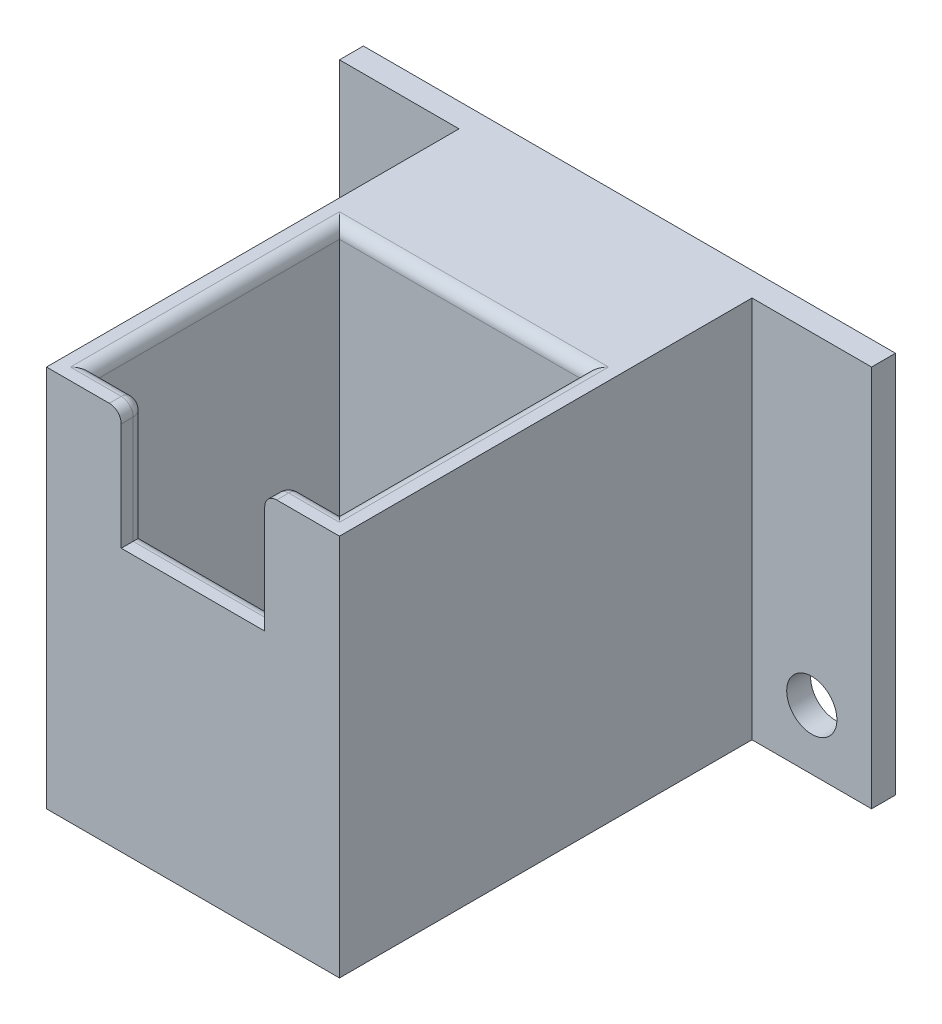
SolidWorks part; units mm, degrees
ref_plane "Plan de face" through (0, 0, 0) normal (0, 0, 1) x (1, 0, 0)
ref_plane "Plan de dessus" through (0, 0, 0) normal (0, 1, 0) x (1, 0, 0)
ref_plane "Plan de droite" through (0, 0, 0) normal (1, 0, 0) x (0, 0, -1)
sketch "Esquisse1" plane through (0, 0, 0) normal (0, 1, 0) x (1, 0, 0)
  line L1 (0, 0) -> (24.5, 0)
  line L2 (0, 0) -> (0, 34.5)
  line L3 (0, 36.5) -> (24.5, 36.5)
  line L4 (24.5, 0) -> (24.5, 34.5)
  line L5 (2, 22.5) -> (22.5, 22.5)
  line L6 (2, 22.5) -> (2, 2)
  line L7 (2, 2) -> (22.5, 2)
  line L8 (22.5, 22.5) -> (22.5, 2)
  line L9 (0, 36.5) -> (-10, 36.5)
  line L11 (0, 34.5) -> (-10, 34.5)
  line L12 (-10, 36.5) -> (-10, 34.5)
  line L13 (24.5, 36.5) -> (34.5, 36.5)
  line L15 (24.5, 34.5) -> (34.5, 34.5)
  line L16 (34.5, 36.5) -> (34.5, 34.5)
  point P9 (12.25, 0)
  point P10 (12.25, 2)
  dimension "D1" = 24.5
  dimension "D2" = 36.5
  dimension "D3" = 20.5
  dimension "D4" = 20.5
  dimension "D5" = 2
  dimension "D6" = 2
  dimension "D7" = 2
  dimension "D8" = 10
  dimension "D9" = 10
extrude "Boss.-Extru.1" add sketch "Esquisse1" along normal blind 32
sketch "Esquisse2" plane through (0, 0, 0) normal (0, -1, 0) x (1, 0, 0)
  line L0 (0, 0) -> (24.5, 0) construction
  line L5 (0, -34.5) -> (0, 0) construction
  line L6 (2, -2) -> (22.5, -22.5) construction
  line L7 (2, -2) -> (22.5, -2)
  line L8 (2, -2) -> (2, -22.5)
  line L9 (2, -22.5) -> (22.5, -22.5)
  line L10 (22.5, -2) -> (22.5, -22.5)
  circle A0 centre (12.25, -12.25) radius 8
  circle A1 centre (3.5, -3.5) radius 1.25
  circle A2 centre (21, -3.5) radius 1.25
  circle A3 centre (21, -21) radius 1.25
  circle A4 centre (3.5, -21) radius 1.25
  point P6 (12.25, 0)
  point P10 (0, -17.25)
  point P25 (12.25, -12.25)
  dimension "D1" = 16
  dimension "D2" = 2.5
  dimension "D3" = 1.5
  dimension "D4" = 4
extrude "Boss.-Extru.2" add sketch "Esquisse2" against normal blind 2
sketch "Esquisse4" plane through (0, 32, 0) normal (0, 1, 0) x (1, 0, 0)
  line L0 (2, 2) -> (22.5, 2) construction
  line L1 (6.25, 2) -> (18.25, 2)
  line L2 (6.25, 2) -> (6.25, 0)
  line L3 (6.25, 0) -> (18.25, 0)
  line L4 (18.25, 2) -> (18.25, 0)
  line L5 (0, 0) -> (24.5, 0) construction
  point P8 (12.25, 0)
  point P9 (12.25, 0)
  dimension "D1" = 12
extrude "Enlèv. mat.-Extru.2" cut sketch "Esquisse4" against normal blind 10
fillet "Congé1" radius 1 10 edges at (18.25, 27, -2) (12.25, 22, -2) (6.25, 27, -2) (4.125, 32, -2) (20.375, 32, -2) (22.5, 32, -12.25) (12.25, 32, -22.5) (2, 32, -12.25) (18.25, 32, -1) (6.25, 32, -1)
sketch "Esquisse5" plane through (0, 0, -36.5) normal (0, 0, -1) x (-1, 0, 0)
  line L0 (-12.25, 32) -> (-12.25, 0) construction
  line L1 (-34.5, 32) -> (10, 32) construction
  line L2 (-34.5, 0) -> (10, 0) construction
  line L3 (-34.5, 32) -> (-34.5, 0) construction
  circle A0 centre (-29.5, 5) radius 2.1
  circle A1 centre (5, 5) radius 2.1
  dimension "D1" = 4.2
  dimension "D2" = 5
  dimension "D3" = 5
extrude "Enlèv. mat.-Extru.3" cut sketch "Esquisse5" against normal up to next
